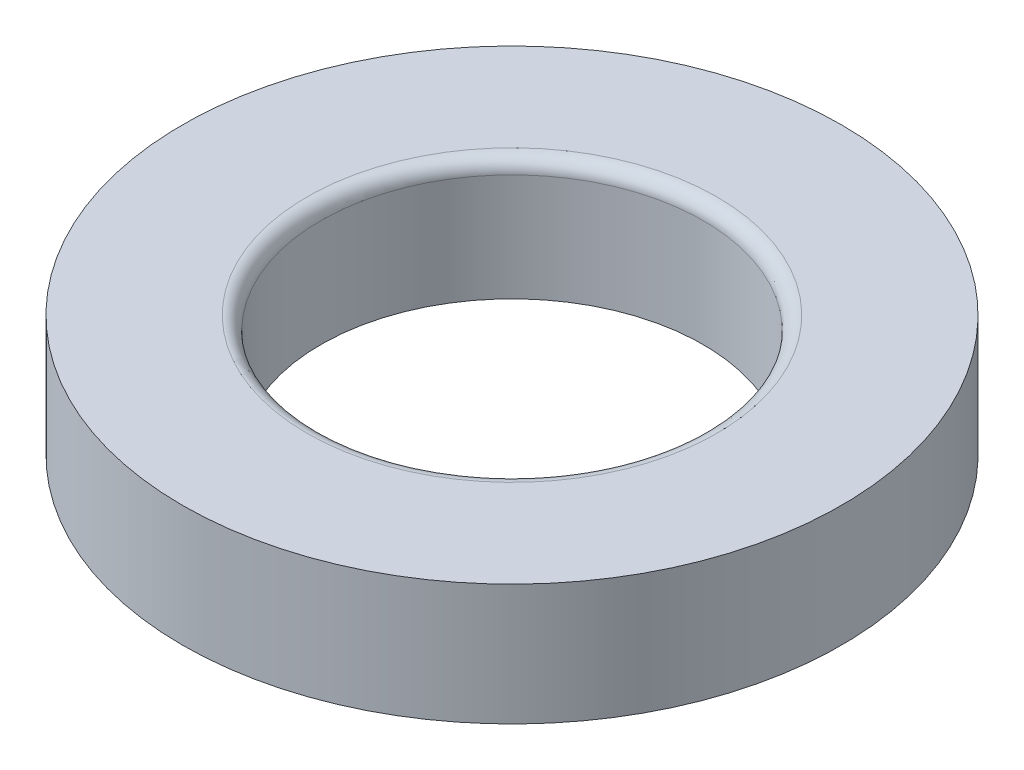
SolidWorks part; units mm, degrees
ref_plane "Front Plane" through (0, 0, 0) normal (0, 0, 1) x (1, 0, 0)
ref_plane "Top Plane" through (0, 0, 0) normal (0, 1, 0) x (1, 0, 0)
ref_plane "Right Plane" through (0, 0, 0) normal (1, 0, 0) x (0, 0, -1)
sketch "Sketch1" plane through (0, 0, 0) normal (0, 1, 0) x (1, 0, 0)
  circle A0 centre (0, 0) radius 11.05
  circle A1 centre (0, 0) radius 19.05
  dimension "D1" = 22.1
  dimension "D2" = 38.1
extrude "Boss-Extrude1" add sketch "Sketch1" along normal mid plane 7
fillet "Fillet1" radius 0.7937 1 edges at (0, 3.5, 11.05)
